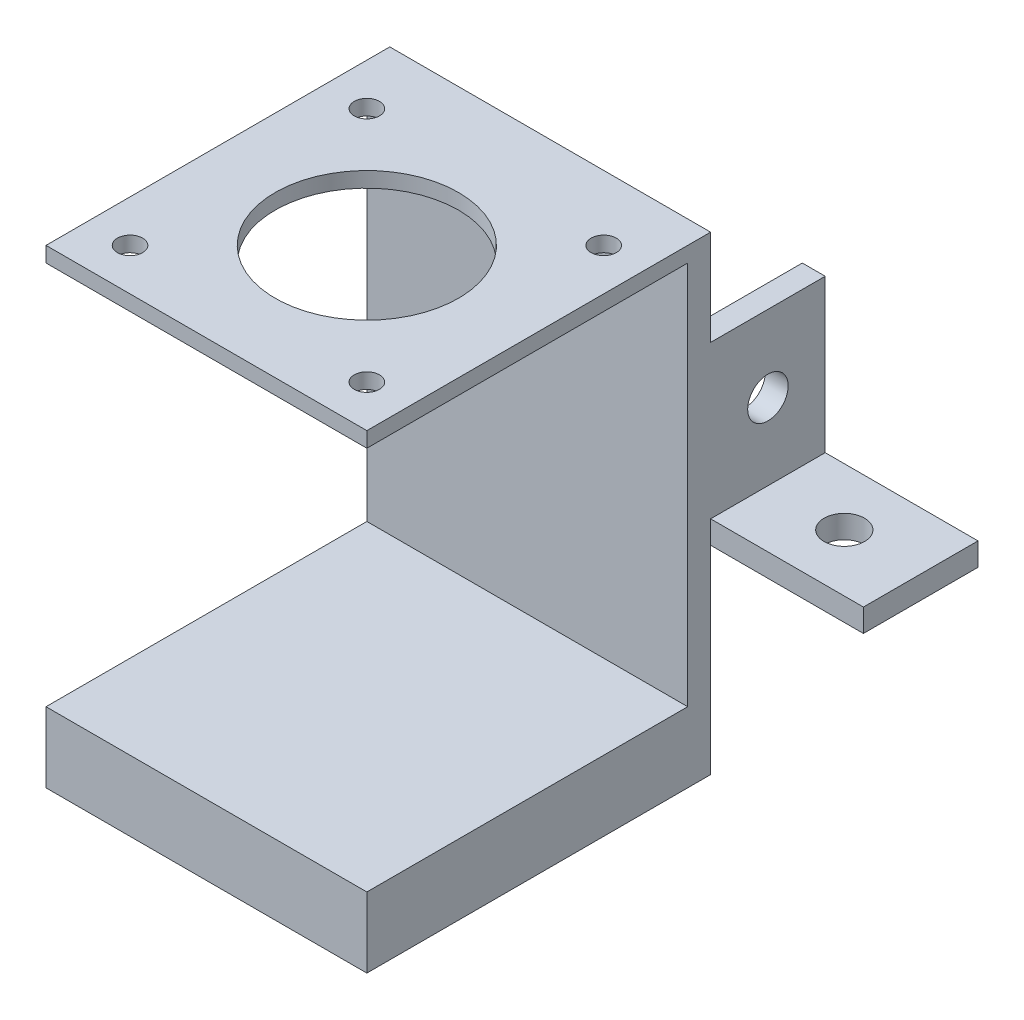
SolidWorks part; units mm, degrees
ref_plane "前视基准面" through (0, 0, 0) normal (0, 0, 1) x (1, 0, 0)
ref_plane "上视基准面" through (0, 0, 0) normal (0, 1, 0) x (1, 0, 0)
ref_plane "右视基准面" through (0, 0, 0) normal (1, 0, 0) x (0, 0, -1)
sketch "草图1" plane through (0, 0, 0) normal (0, 0, 1) x (1, 0, 0)
  line L1 (-18.194, 11.3599) -> (23.806, 11.3599)
  line L2 (-18.194, 11.3599) -> (-18.194, -50.1401)
  line L3 (-18.194, -50.1401) -> (23.806, -50.1401)
  line L4 (23.806, 11.3599) -> (23.806, -50.1401)
  dimension "D1" = 42
  dimension "D2" = 61.5
extrude "凸台-拉伸1" add sketch "草图1" along normal blind 3
sketch "草图2" plane through (0, 0, 3) normal (0, 0, 1) x (1, 0, 0)
  line L1 (23.806, -50.1401) -> (23.806, 11.3599) construction
  line L2 (-18.194, -50.1401) -> (23.806, -50.1401)
  line L3 (-18.194, -50.1401) -> (-18.194, -40.9401)
  line L4 (-18.194, -40.9401) -> (23.806, -40.9401)
  line L5 (23.806, -50.1401) -> (23.806, -40.9401)
  line L7 (-18.194, 11.3599) -> (23.806, 11.3599)
  line L8 (-18.194, 11.3599) -> (-18.194, 9.3599)
  line L9 (-18.194, 9.3599) -> (23.806, 9.3599)
  line L10 (23.806, 11.3599) -> (23.806, 9.3599)
  dimension "D1" = 9.2
  dimension "D2" = 2
extrude "凸台-拉伸2" add sketch "草图2" along normal blind 42
sketch "草图3" plane through (0, 9.3599, 0) normal (0, -1, 0) x (1, 0, 0)
  line L0 (-18.194, 45) -> (23.806, 45) construction
  line L1 (23.806, 45) -> (23.806, 3) construction
  circle A0 centre (2.806, 24) radius 12
  circle A1 centre (18.306, 39.5) radius 1.65
  circle A2 centre (18.306, 8.5) radius 1.65
  circle A3 centre (-12.694, 8.5) radius 1.65
  circle A4 centre (-12.694, 39.5) radius 1.65
  point P17 (2.806, 24)
  dimension "D1" = 24
  dimension "D2" = 3.3
  dimension "D3" = 5.5
  dimension "D4" = 5.5
  dimension "D5" = 4
extrude "切除-拉伸1" cut sketch "草图3" against normal through all
sketch "草图4" plane through (0, 0, 0) normal (0, 0, -1) x (-1, 0, 0)
  line L0 (-23.806, -50.1401) -> (-23.806, 11.3599) construction
  line L2 (-23.806, -21.1401) -> (-23.806, -1.1401)
  line L3 (-23.806, -1.1401) -> (-20.806, -1.1401)
  line L4 (-20.806, -21.1401) -> (-20.806, -1.1401)
  line L8 (-23.806, -21.1401) -> (-23.806, -24.1401)
  line L9 (-23.806, -24.1401) -> (-20.806, -24.1401)
  line L10 (-20.806, -21.1401) -> (-20.806, -24.1401)
  dimension "D2" = 20
  dimension "D3" = 3
  dimension "D4" = 3
extrude "凸台-拉伸3" add sketch "草图4" along normal blind 15
sketch "草图6" plane through (20.806, 0, 0) normal (-1, 0, 0) x (0, 0, 1)
  circle A0 centre (-7.5, -11.1401) radius 2.65
  dimension "D1" = 5.3
extrude "切除-拉伸2" cut sketch "草图6" against normal blind 5
sketch "草图7" plane through (23.806, 0, 0) normal (1, 0, 0) x (0, 0, -1)
  line L1 (15, -24.1401) -> (0, -24.1401)
  line L2 (15, -24.1401) -> (15, -21.1401)
  line L3 (15, -21.1401) -> (0, -21.1401)
  line L4 (0, -24.1401) -> (0, -21.1401)
  dimension "D1" = 3
extrude "凸台-拉伸4" add sketch "草图7" along normal blind 20
sketch "草图8" plane through (0, -21.1401, 0) normal (0, 1, 0) x (1, 0, 0)
  circle A0 centre (33.806, 7.5) radius 2.65
  dimension "D1" = 5.3
extrude "切除-拉伸3" cut sketch "草图8" against normal blind 20
